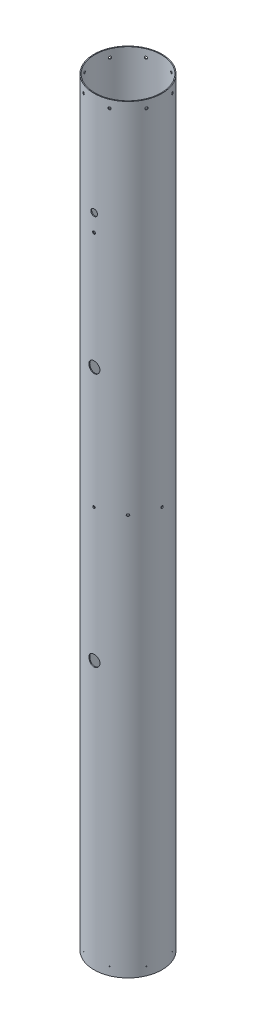
SolidWorks part; units mm, degrees
material "Thornel Mat VMA"
ref_plane "Ebene vorne" through (0, 0, 0) normal (0, 0, 1) x (1, 0, 0)
ref_plane "Ebene oben" through (0, 0, 0) normal (0, 1, 0) x (1, 0, 0)
ref_plane "Ebene rechts" through (0, 0, 0) normal (1, 0, 0) x (0, 0, -1)
sketch "Skizze1" plane through (0, 0, 0) normal (0, 1, 0) x (1, 0, 0)
  circle A0 centre (0, 0) radius 60
  dimension "D1" = 120
extrude "Körperrohr" add sketch "Skizze1" along normal blind 1370 thin
ref_plane "CouplerHoles" through (-23.535, 0, 56.8186) normal (-0.3827, 0, 0.9239) x (0, -1, 0)
sketch "Sketch1" plane through (-23.535, 0, 56.8186) normal (0.3827, 0, -0.9239) x (-0.9239, 0, -0.3827)
  line L0 (61.5, 1370) -> (-61.5, 1370) construction
  circle A0 centre (0, 12.65) radius 0.75
  circle A1 centre (0, 1356) radius 2.25
  dimension "D2" = 1.5
  dimension "D3" = 4.5
  dimension "D1" = 12.65
  dimension "D4" = 14
extrude "Cut-Extrude1" cut sketch "Sketch1" along normal up to next
pattern_circular "CirPattern1" count 8 over 360 about axis through (0, 1370, 0) along (0, -1, 0) of "Cut-Extrude1"
ref_plane "RailbuttonHole" through (61.5, 0, 0) normal (1, 0, 0) x (0, 0, -1)
sketch "Sketch3" plane through (61.5, 0, 0) normal (1, 0, 0) x (0, 0, -1)
  circle A0 centre (0, 722.3) radius 2.25
  dimension "D1" = 4.5
  dimension "D2" = 722.3
extrude "Cut-Extrude3" cut sketch "Sketch3" against normal up to next
pattern_circular "CirPattern2" count 8 over 360 about axis through (0, 1370, 0) along (0, -1, 0) of "Cut-Extrude3"
ref_plane "UmbilicalHoles" through (0, 0, 61.5) normal (0, 0, 1) x (1, 0, 0)
sketch "Sketch2" plane through (0, 0, 61.5) normal (0, 0, 1) x (1, 0, 0)
  line L0 (60, 1370) -> (-60, 1370) construction
  circle A0 centre (0, 482) radius 10
  circle A1 centre (0, 941.3) radius 10
  circle A2 centre (0, 722.3) radius 2.25 construction
  circle A3 centre (0, 1152) radius 2.5
  dimension "D1" = 20
  dimension "D3" = 219
  dimension "D6" = 5
  dimension "D2" = 482
  dimension "D5" = 218
extrude "Cut-Extrude2" cut sketch "Sketch2" against normal up to next
sketch "Sketch4" plane through (0, 0, 61.5) normal (0, 0, 1) x (1, 0, 0)
  line L0 (60, 1370) -> (-60, 1370) construction
  circle A0 centre (0, 1183.43) radius 6
  dimension "D2" = 12
  dimension "D1" = 186.57
extrude "Cut-Extrude4" cut sketch "Sketch4" against normal through all
ref_plane "Plane1" through (-61.5, 0, 0) normal (-1, 0, 0) x (0, 0, 1)
sketch "Sketch5" plane through (-61.5, 0, 0) normal (-1, 0, 0) x (0, 0, 1)
  line L0 (-61.5, 0) -> (61.5, 0) construction
  circle A0 centre (0, 497) radius 4
  dimension "D2" = 8
  dimension "D1" = 497
extrude "Cut-Extrude5" cut sketch "Sketch5" against normal up to next
sketch "Skizze2" plane through (0, 0, 0) normal (0, -1, 0) x (1, 0, 0)
  circle A0 centre (0, 0) radius 60
  circle A1 centre (0, 0) radius 61.5
extrude "Aufsatz-Linear austragen1" add sketch "Skizze2" along normal blind 2.35
